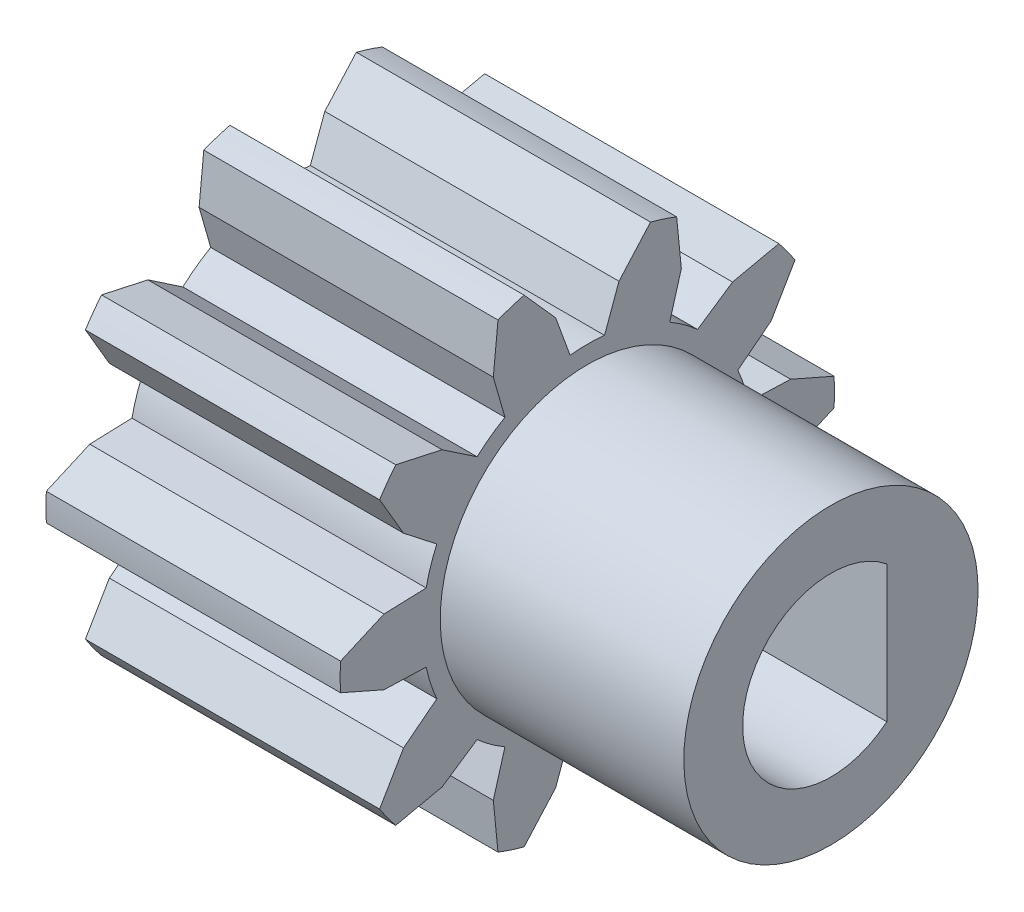
SolidWorks part; units mm, degrees
ref_plane "Plan de face" through (0, 0, 0) normal (0, 0, 1) x (1, 0, 0)
ref_plane "Plan de dessus" through (0, 0, 0) normal (0, 1, 0) x (1, 0, 0)
ref_plane "Plan de droite" through (0, 0, 0) normal (1, 0, 0) x (0, 0, -1)
ref_plane "Plan1" through (0, 0, 0) normal (0, 0, -1) x (-1, 0, 0)
sketch "Esquisse1" plane through (0, 0, 0) normal (0, 0, -1) x (-1, 0, 0)
  line L0 (-2.5, 4.2) -> (-2.5, 0)
  line L1 (-2.5, 0) -> (2.5, 0)
  line L2 (2.5, 0) -> (2.5, 4.2)
  line L3 (2.5, 4.2) -> (-2.5, 4.2)
  line L4 (-2.5, 0) -> (2.5, 0) construction
revolve "Révolution1" add sketch "Esquisse1" angle 360 about L4
sketch "Esquisse2" plane through (-2.5, 0, 0) normal (-1, 0, 0) x (0, 0, 1)
  line L0 (4.1935, -0.2333) -> (2.7147, -0.8821)
  line L1 (2.7147, -0.8821) -> (3.5298, -2.2761)
  arc A0 (3.5298, -2.2761) -> (4.1935, -0.2333) centre (0, 0) ccw
extrude "Enlèv. mat.-Extru.1" cut sketch "Esquisse2" against normal through all
sketch "Esquisse3" plane through (-2.5, 0, 0) normal (-1, 0, 0) x (0, 0, 1)
  line L0 (2.5579, -1.1389) -> (3.1229, -1.5803)
  line L1 (3.1229, -1.5803) -> (2.7147, -0.8821)
  line L2 (2.7147, -0.8821) -> (3.4554, -0.5571)
  line L3 (3.4554, -0.5571) -> (2.7388, -0.5822)
  arc A0 (2.7388, -0.5822) -> (2.5579, -1.1389) centre (0, 0) cw
extrude "Enlèv. mat.-Extru.2" cut sketch "Esquisse3" against normal through all
sketch "Esquisse4" plane through (-2.5, 0, 0) normal (-1, 0, 0) x (0, 0, 1)
  line L0 (3.2555, -2.6537) -> (1.6778, -2.3092)
  line L1 (1.6778, -2.3092) -> (1.5178, -3.9162)
  arc A0 (1.5178, -3.9162) -> (3.2555, -2.6537) centre (0, 0) ccw
extrude "Enlèv. mat.-Extru.3" cut sketch "Esquisse4" against normal through all
sketch "Esquisse5" plane through (-2.5, 0, 0) normal (-1, 0, 0) x (0, 0, 1)
  line L0 (1.4, -2.4249) -> (1.5976, -3.1141)
  line L1 (1.5976, -3.1141) -> (1.6778, -2.3092)
  line L2 (1.6778, -2.3092) -> (2.468, -2.4817)
  line L3 (2.468, -2.4817) -> (1.8736, -2.0808)
  arc A0 (1.8736, -2.0808) -> (1.4, -2.4249) centre (0, 0) cw
extrude "Enlèv. mat.-Extru.4" cut sketch "Esquisse5" against normal through all
sketch "Esquisse6" plane through (-2.5, 0, 0) normal (-1, 0, 0) x (0, 0, 1)
  line L0 (1.074, -4.0604) -> (0, -2.8544)
  line L1 (0, -2.8544) -> (-1.074, -4.0604)
  arc A0 (-1.074, -4.0604) -> (1.074, -4.0604) centre (0, 0) ccw
extrude "Enlèv. mat.-Extru.5" cut sketch "Esquisse6" against normal through all
sketch "Esquisse7" plane through (-2.5, 0, 0) normal (-1, 0, 0) x (0, 0, 1)
  line L0 (-0.2927, -2.7847) -> (-0.5379, -3.4584)
  line L1 (-0.5379, -3.4584) -> (0, -2.8544)
  line L2 (0, -2.8544) -> (0.5379, -3.4584)
  line L3 (0.5379, -3.4584) -> (0.2927, -2.7847)
  arc A0 (0.2927, -2.7847) -> (-0.2927, -2.7847) centre (0, 0) cw
extrude "Enlèv. mat.-Extru.6" cut sketch "Esquisse7" against normal through all
sketch "Esquisse8" plane through (-2.5, 0, 0) normal (-1, 0, 0) x (0, 0, 1)
  line L0 (-1.5178, -3.9162) -> (-1.6778, -2.3092)
  line L1 (-1.6778, -2.3092) -> (-3.2555, -2.6537)
  arc A0 (-3.2555, -2.6537) -> (-1.5178, -3.9162) centre (0, 0) ccw
extrude "Enlèv. mat.-Extru.7" cut sketch "Esquisse8" against normal through all
sketch "Esquisse9" plane through (-2.5, 0, 0) normal (-1, 0, 0) x (0, 0, 1)
  line L0 (-1.8736, -2.0808) -> (-2.468, -2.4817)
  line L1 (-2.468, -2.4817) -> (-1.6778, -2.3092)
  line L2 (-1.6778, -2.3092) -> (-1.5976, -3.1141)
  line L3 (-1.5976, -3.1141) -> (-1.4, -2.4249)
  arc A0 (-1.4, -2.4249) -> (-1.8736, -2.0808) centre (0, 0) cw
extrude "Enlèv. mat.-Extru.8" cut sketch "Esquisse9" against normal through all
sketch "Esquisse10" plane through (-2.5, 0, 0) normal (-1, 0, 0) x (0, 0, 1)
  line L0 (-3.5298, -2.2761) -> (-2.7147, -0.8821)
  line L1 (-2.7147, -0.8821) -> (-4.1935, -0.2333)
  arc A0 (-4.1935, -0.2333) -> (-3.5298, -2.2761) centre (0, 0) ccw
extrude "Enlèv. mat.-Extru.9" cut sketch "Esquisse10" against normal through all
sketch "Esquisse11" plane through (-2.5, 0, 0) normal (-1, 0, 0) x (0, 0, 1)
  line L0 (-2.7388, -0.5822) -> (-3.4554, -0.5571)
  line L1 (-3.4554, -0.5571) -> (-2.7147, -0.8821)
  line L2 (-2.7147, -0.8821) -> (-3.1229, -1.5803)
  line L3 (-3.1229, -1.5803) -> (-2.5579, -1.1389)
  arc A0 (-2.5579, -1.1389) -> (-2.7388, -0.5822) centre (0, 0) cw
extrude "Enlèv. mat.-Extru.10" cut sketch "Esquisse11" against normal through all
sketch "Esquisse12" plane through (-2.5, 0, 0) normal (-1, 0, 0) x (0, 0, 1)
  line L0 (-4.1935, 0.2333) -> (-2.7147, 0.8821)
  line L1 (-2.7147, 0.8821) -> (-3.5298, 2.2761)
  arc A0 (-3.5298, 2.2761) -> (-4.1935, 0.2333) centre (0, 0) ccw
extrude "Enlèv. mat.-Extru.11" cut sketch "Esquisse12" against normal through all
sketch "Esquisse13" plane through (-2.5, 0, 0) normal (-1, 0, 0) x (0, 0, 1)
  line L0 (-2.7147, 0.8821) -> (-3.4554, 0.5571)
  line L1 (-3.4554, 0.5571) -> (-2.7388, 0.5822)
  line L2 (-2.5579, 1.1389) -> (-3.1229, 1.5803)
  line L3 (-3.1229, 1.5803) -> (-2.7147, 0.8821)
  arc A0 (-2.7388, 0.5822) -> (-2.5579, 1.1389) centre (0, 0) cw
extrude "Enlèv. mat.-Extru.12" cut sketch "Esquisse13" against normal through all
sketch "Esquisse14" plane through (-2.5, 0, 0) normal (-1, 0, 0) x (0, 0, 1)
  line L0 (-3.2555, 2.6537) -> (-1.6778, 2.3092)
  line L1 (-1.6778, 2.3092) -> (-1.5178, 3.9162)
  arc A0 (-1.5178, 3.9162) -> (-3.2555, 2.6537) centre (0, 0) ccw
extrude "Enlèv. mat.-Extru.13" cut sketch "Esquisse14" against normal through all
sketch "Esquisse15" plane through (-2.5, 0, 0) normal (-1, 0, 0) x (0, 0, 1)
  line L0 (-1.6778, 2.3092) -> (-2.468, 2.4817)
  line L1 (-2.468, 2.4817) -> (-1.8736, 2.0808)
  line L2 (-1.4, 2.4249) -> (-1.5976, 3.1141)
  line L3 (-1.5976, 3.1141) -> (-1.6778, 2.3092)
  arc A0 (-1.8736, 2.0808) -> (-1.4, 2.4249) centre (0, 0) cw
extrude "Enlèv. mat.-Extru.14" cut sketch "Esquisse15" against normal through all
sketch "Esquisse16" plane through (-2.5, 0, 0) normal (-1, 0, 0) x (0, 0, 1)
  line L0 (-1.074, 4.0604) -> (0, 2.8544)
  line L1 (0, 2.8544) -> (1.074, 4.0604)
  arc A0 (1.074, 4.0604) -> (-1.074, 4.0604) centre (0, 0) ccw
extrude "Enlèv. mat.-Extru.15" cut sketch "Esquisse16" against normal through all
sketch "Esquisse17" plane through (-2.5, 0, 0) normal (-1, 0, 0) x (0, 0, 1)
  line L0 (0, 2.8544) -> (-0.5379, 3.4584)
  line L1 (-0.5379, 3.4584) -> (-0.2927, 2.7847)
  line L2 (0.2927, 2.7847) -> (0.5379, 3.4584)
  line L3 (0.5379, 3.4584) -> (0, 2.8544)
  arc A0 (-0.2927, 2.7847) -> (0.2927, 2.7847) centre (0, 0) cw
extrude "Enlèv. mat.-Extru.16" cut sketch "Esquisse17" against normal through all
sketch "Esquisse18" plane through (-2.5, 0, 0) normal (-1, 0, 0) x (0, 0, 1)
  line L0 (1.5178, 3.9162) -> (1.6778, 2.3092)
  line L1 (1.6778, 2.3092) -> (3.2555, 2.6537)
  arc A0 (3.2555, 2.6537) -> (1.5178, 3.9162) centre (0, 0) ccw
extrude "Enlèv. mat.-Extru.17" cut sketch "Esquisse18" against normal through all
sketch "Esquisse19" plane through (-2.5, 0, 0) normal (-1, 0, 0) x (0, 0, 1)
  line L0 (1.6778, 2.3092) -> (1.5976, 3.1141)
  line L1 (1.5976, 3.1141) -> (1.4, 2.4249)
  line L2 (1.8736, 2.0808) -> (2.468, 2.4817)
  line L3 (2.468, 2.4817) -> (1.6778, 2.3092)
  arc A0 (1.4, 2.4249) -> (1.8736, 2.0808) centre (0, 0) cw
extrude "Enlèv. mat.-Extru.18" cut sketch "Esquisse19" against normal through all
sketch "Esquisse20" plane through (-2.5, 0, 0) normal (-1, 0, 0) x (0, 0, 1)
  line L0 (3.5298, 2.2761) -> (2.7147, 0.8821)
  line L1 (2.7147, 0.8821) -> (4.1935, 0.2333)
  arc A0 (4.1935, 0.2333) -> (3.5298, 2.2761) centre (0, 0) ccw
extrude "Enlèv. mat.-Extru.19" cut sketch "Esquisse20" against normal through all
sketch "Esquisse21" plane through (-2.5, 0, 0) normal (-1, 0, 0) x (0, 0, 1)
  line L0 (2.7147, 0.8821) -> (3.1229, 1.5803)
  line L1 (3.1229, 1.5803) -> (2.5579, 1.1389)
  line L2 (2.7388, 0.5822) -> (3.4554, 0.5571)
  line L3 (3.4554, 0.5571) -> (2.7147, 0.8821)
  arc A0 (2.5579, 1.1389) -> (2.7388, 0.5822) centre (0, 0) cw
extrude "Enlèv. mat.-Extru.20" cut sketch "Esquisse21" against normal through all
sketch "Esquisse22" plane through (0, 0, 0) normal (0, 0, -1) x (-1, 0, 0)
  line L0 (-6.64, 2.5) -> (-6.64, 0)
  line L1 (-6.64, 0) -> (-2.5, 0)
  line L2 (-2.5, 0) -> (-2.5, 2.5)
  line L3 (-2.5, 2.5) -> (-6.64, 2.5)
  line L4 (-6.64, 0) -> (-2.5, 0) construction
  dimension "D1" = 4.14
  dimension "D2" = 2.5
revolve "Révolution2" add sketch "Esquisse22" angle 360 about L4
sketch "Esquisse28" plane through (0, 0, 0) normal (1, 0, 0) x (0, 0, -1)
  circle A0 centre (0, 0) radius 3.6154
  dimension "D1" = 7.2309
sketch "Esquisse29" plane through (-2.5, 0, 0) normal (-1, 0, 0) x (0, 0, 1)
  circle A0 centre (0, 0) radius 1.5
  dimension "D1" = 3
extrude "Enlèv. mat.-Extru.21" cut sketch "Esquisse29" against normal blind 10
sketch "Esquisse31" plane through (-2.5, 0, 0) normal (-1, 0, 0) x (0, 0, 1)
  line L1 (-0.95, 0) -> (-0.95, 1.1608)
  line L2 (-0.95, 0) -> (-0.95, -1.1608)
  circle A0 centre (0, 0) radius 1.5 construction
  arc A1 (-0.95, -1.1608) -> (-0.95, 1.1608) centre (0, 0) cw
extrude "Boss.-Extru.1" add sketch "Esquisse31" against normal blind 9.14
